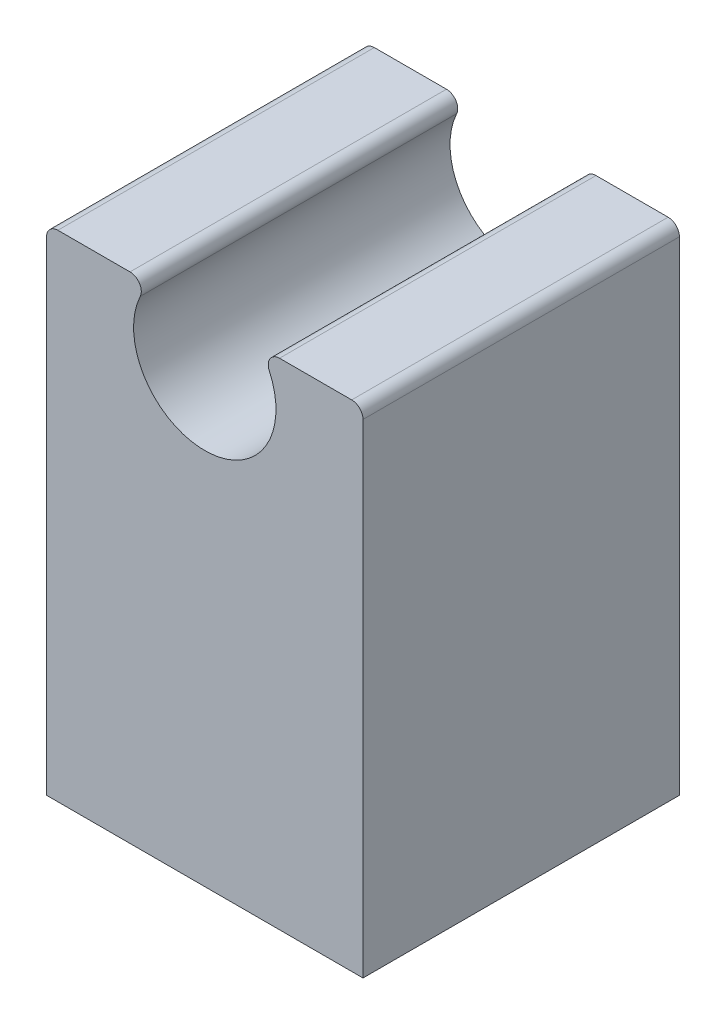
SolidWorks part; units mm, degrees
ref_plane "Front Plane" through (0, 0, 0) normal (0, 0, 1) x (1, 0, 0)
ref_plane "Top Plane" through (0, 0, 0) normal (0, 1, 0) x (1, 0, 0)
ref_plane "Right Plane" through (0, 0, 0) normal (1, 0, 0) x (0, 0, -1)
sketch "Sketch1" plane through (0, 0, 0) normal (0, 0, 1) x (1, 0, 0)
  line L0 (0, 0) -> (0, -30) construction
  line L1 (-11.1125, 2.4485) -> (-11.1125, -30)
  line L2 (-11.1125, -30) -> (0, -30)
  line L3 (-10.3187, 3.2423) -> (-5.2509, 3.2423)
  line L4 (-4.5315, 2.1131) -> (0, 0) construction
  line L5 (0, -5) -> (0, -30)
  arc A0 (-4.5315, 2.1131) -> (0, -5) centre (0, 0) ccw
  arc A1 (-4.5315, 2.1131) -> (-5.2509, 3.2423) centre (-5.2509, 2.4485) ccw
  arc A2 (-10.3187, 3.2423) -> (-11.1125, 2.4485) centre (-10.3187, 2.4485) ccw
  dimension "D1" = 0.7937
  dimension "D2" = 5
  dimension "D3" = 115
  dimension "D4" = 11.1125
  dimension "D5" = 25
extrude "Boss-Extrude1" add sketch "Sketch1" along normal mid plane 22.225
mirror "Mirror1" about plane through (0, 0, 0) normal (1, 0, 0) of "Boss-Extrude1"
sketch "Sketch2" plane through (0, -30, 0) normal (0, -1, 0) x (1, 0, 0)
  line L4 (-11.1125, -11.1125) -> (11.1125, -11.1125)
  line L5 (11.1125, -11.1125) -> (11.1125, 11.1125)
  line L6 (11.1125, 11.1125) -> (-11.1125, 11.1125)
  line L7 (-11.1125, 11.1125) -> (-11.1125, -11.1125)
  line L8 (-11.1125, -11.1125) -> (11.1125, -11.1125)
  line L9 (11.1125, -11.1125) -> (11.1125, 11.1125)
  line L10 (11.1125, 11.1125) -> (-11.1125, 11.1125)
  line L11 (-11.1125, 11.1125) -> (-11.1125, -11.1125)
  dimension "D1" = 0
extrude "Boss-Extrude2" add sketch "Sketch2" along normal blind 1.524
